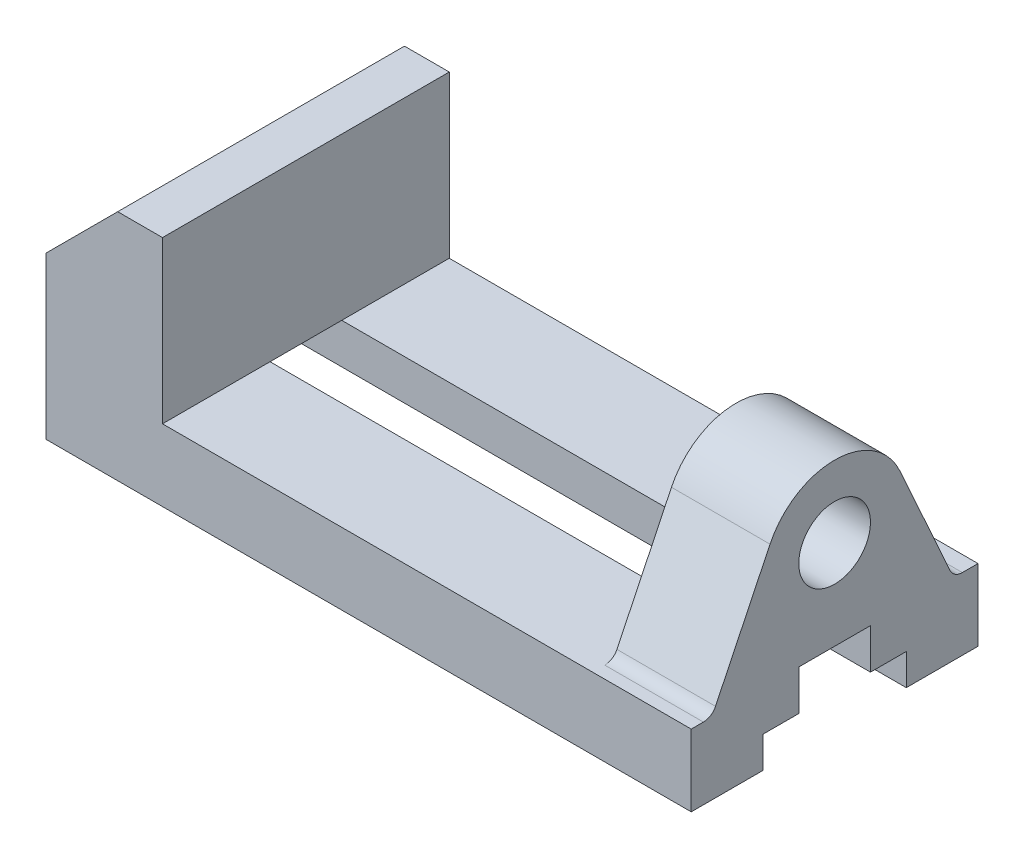
SolidWorks part; units mm, degrees
ref_plane "Front Plane" through (0, 0, 0) normal (0, 0, 1) x (1, 0, 0)
ref_plane "Top Plane" through (0, 0, 0) normal (0, 1, 0) x (1, 0, 0)
ref_plane "Right Plane" through (0, 0, 0) normal (1, 0, 0) x (0, 0, -1)
sketch "Sketch1" plane through (0, 0, 0) normal (0, 1, 0) x (1, 0, 0)
  line L1 (72, -32) -> (-72, -32)
  line L2 (72, -32) -> (72, 32)
  line L3 (72, 32) -> (-72, 32)
  line L4 (-72, -32) -> (-72, 32)
  line L5 (72, -32) -> (-72, 32) construction
  line L6 (72, 32) -> (-72, -32) construction
  point P0 (0, 0)
  dimension "D1" = 64
  dimension "D2" = 144
extrude "Boss-Extrude1" add sketch "Sketch1" along normal blind 16
sketch "Sketch2" plane through (72, 0, 0) normal (1, 0, 0) x (0, 0, -1)
  line L0 (0, 0) -> (0, 16) construction
  line L1 (-32, 0) -> (32, 0) construction
  line L2 (-32, 16) -> (32, 16) construction
  line L3 (-16, 0) -> (-16, 7)
  line L4 (-16, 7) -> (-8, 7)
  line L5 (-8, 7) -> (-8, 16)
  line L6 (-8, 16) -> (8, 16)
  line L7 (-32, 16) -> (-32, 0) construction
  line L8 (-16, 0) -> (16, 0)
  line L9 (8, 7) -> (8, 16)
  line L10 (16, 7) -> (8, 7)
  line L11 (16, 0) -> (16, 7)
  dimension "D1" = 16
  dimension "D2" = 7
  dimension "D3" = 8
sketch "Sketch3" plane through (0, 16, 0) normal (0, 1, 0) x (1, 0, 0)
  line L0 (-72, 32) -> (-46, 32)
  line L1 (72, 32) -> (-72, 32) construction
  line L2 (-46, 32) -> (-46, -32)
  line L3 (-72, -32) -> (72, -32) construction
  line L4 (-46, -32) -> (-72, -32)
  line L5 (-72, -32) -> (-72, 32)
  dimension "D1" = 26
extrude "Boss-Extrude2" add sketch "Sketch3" along normal blind 36 contours L5 L0 L2 L4
chamfer "Chamfer1" distance 16 1 edges at (-72, 52, 0)
extrude "Cut-Extrude1" cut sketch "Sketch2" against normal up to next
sketch "Sketch5" plane through (72, 0, 0) normal (1, 0, 0) x (0, 0, -1)
  line L0 (-14.4132, 42.9469) -> (-27.401, 16)
  line L1 (-8, 16) -> (-32, 16) construction
  line L2 (14.5862, 42.5758) -> (26.5672, 16)
  line L3 (8, 16) -> (32, 16) construction
  line L4 (-27.401, 16) -> (26.5672, 16)
  circle A0 centre (0, 36) radius 8
  arc A1 (14.5862, 42.5758) -> (-14.4132, 42.9469) centre (0, 36) ccw
  dimension "D1" = 36
  dimension "D2" = 50
extrude "Boss-Extrude3" add sketch "Sketch5" against normal blind 22
fillet "Fillet1" radius 3 2 edges at (61, 16, -26.5672) (61, 16, 27.401)
sketch "Sketch8" plane through (0, 0, 0) normal (0, -1, 0) x (-1, 0, 0)
  line L0 (72, -22) -> (-72, -22) construction
  line L1 (72, -16) -> (72, -32) construction
  line L2 (-72, -32) -> (-72, -16) construction
  line L3 (-34, -32) -> (-34, 42.7947) construction
  line L4 (72, -32) -> (-72, -32) construction
  line L7 (-34, 32) -> (-34, -42.7947) construction
  line L8 (72, 22) -> (-72, 22) construction
  line L9 (36, -32) -> (36, 32) construction
  line L10 (-72, 32) -> (72, 32) construction
  dimension "D1" = 38
  dimension "D2" = 10
  dimension "D3" = 70
hole_wizard "Tap Drill for M6 Helicoil2" positions "3DSketch1" profile "Sketch9" hole size "M6x1.0" standard "ANSI Metric"
sketch3d "3DSketch1"
  line L0 (-72, 0, 22) -> (72, 0, 22) construction
  line L1 (-36, 0, 32) -> (-36, 0, -32) construction
  line L2 (34, 0, 32) -> (34, 0, -42.7947) construction
  line L3 (-72, 0, -22) -> (72, 0, -22) construction
  point P0 (-36, 0, 22)
  point P6 (34, 0, 22)
  point P10 (-36, 0, -22)
  point P14 (34, 0, -22)
sketch "Sketch9" plane through (-36, 0, 22) normal (1, 0, 0) x (0, 0, -1)
  line L0 (0, 0) -> (0, 11.8777)
  line L1 (0, 11.8777) -> (3.125, 10)
  line L2 (3.125, 10) -> (3.125, 0)
  line L5 (3.125, 0) -> (0, 0)
  line L10 (0, 11.8777) -> (-3.125, 10) construction
  line L11 (0, -6.35) -> (0, 107.95) construction
  dimension "Hole Dia." = 6.25
  dimension "Hole Depth" = 10
  dimension "Drill Angle" = 118
